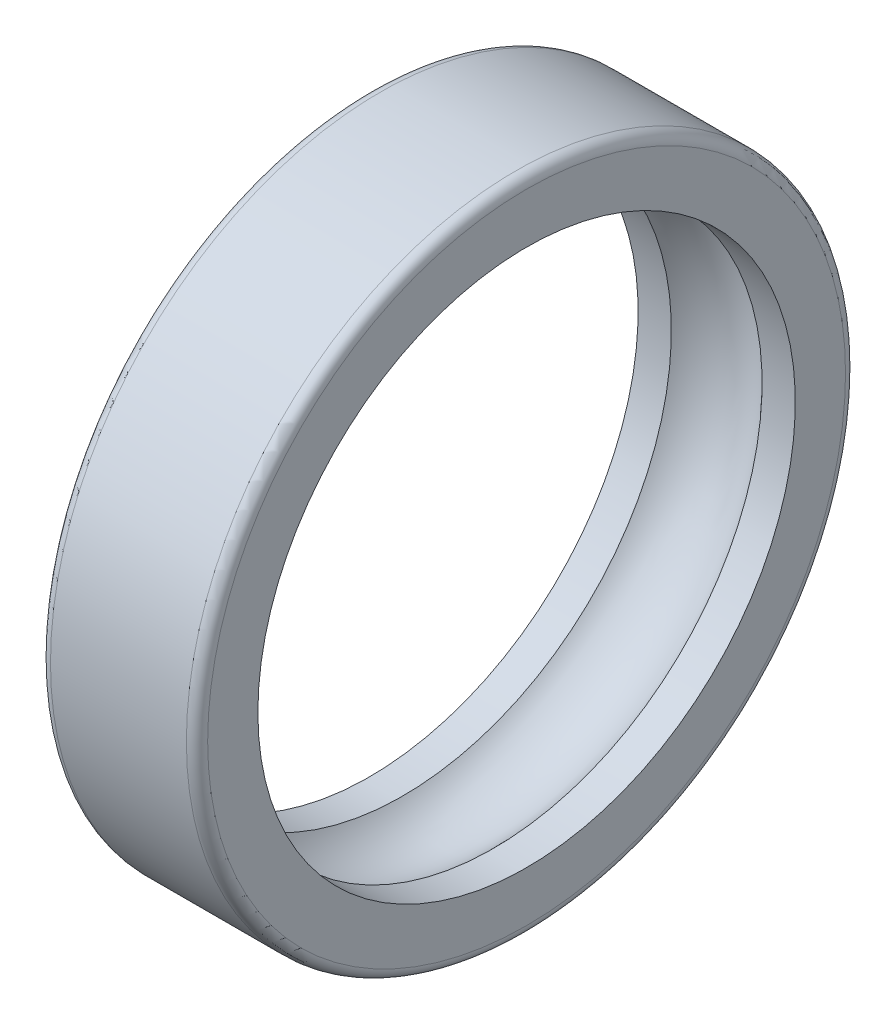
SolidWorks part; units mm, degrees
ref_plane "Front Plane" through (0, 0, 0) normal (0, 0, 1) x (1, 0, 0)
ref_plane "Top Plane" through (0, 0, 0) normal (0, 1, 0) x (1, 0, 0)
ref_plane "Right Plane" through (0, 0, 0) normal (1, 0, 0) x (0, 0, -1)
sketch "Sketch1" plane through (0, 0, 0) normal (0, 0, 1) x (1, 0, 0)
  line L0 (-20.2526, 0) -> (23.787, 0) construction
  line L1 (0, 53) -> (0, 0) construction
  line L2 (-15.5, 65) -> (15.5, 65)
  line L3 (-15.5, 65) -> (-15.5, 53)
  line L4 (-15.5, 53) -> (-8.9443, 53)
  line L5 (15.5, 65) -> (15.5, 53)
  line L6 (-15.5, 65) -> (15.5, 53) construction
  line L7 (-15.5, 53) -> (15.5, 65) construction
  line L8 (8.9443, 53) -> (15.5, 53)
  arc A0 (-8.9443, 53) -> (8.9443, 53) centre (0, 45) cw
  point P3 (0, 59)
  dimension "D5" = 12
  dimension "D1" = 31
  dimension "D2" = 53
  dimension "D3" = 65
  dimension "D4" = 8
revolve "Revolve1" add sketch "Sketch1" angle 360 about L0
fillet "Fillet1" radius 2.1 2 edges at (-15.5, 0, 65) (15.5, 0, 65)
